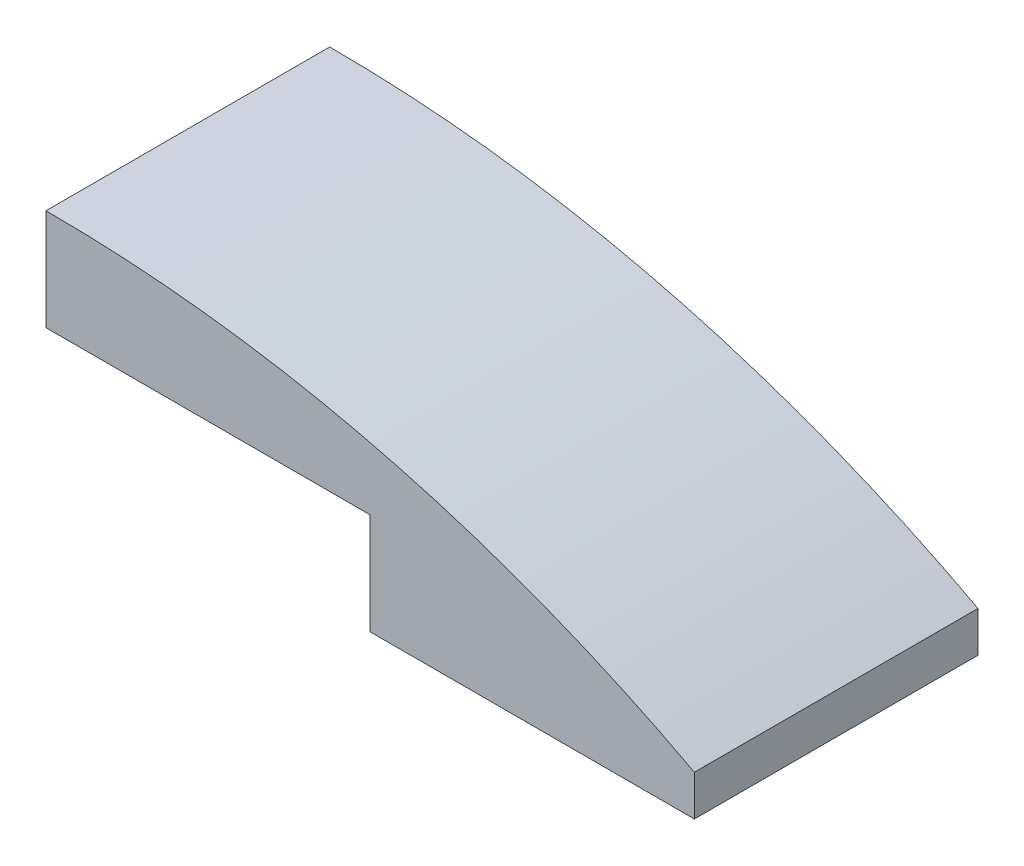
SolidWorks part; units mm, degrees
material "ABS"
ref_plane "Front Plane" through (0, 0, 0) normal (0, 0, 1) x (1, 0, 0)
ref_plane "Top Plane" through (0, 0, 0) normal (0, 1, 0) x (1, 0, 0)
ref_plane "Right Plane" through (0, 0, 0) normal (1, 0, 0) x (0, 0, -1)
sketch "Sketch1" plane through (0, 0, 0) normal (0, 0, 1) x (1, 0, 0)
  line L0 (-10.16, 0) -> (-10.16, 3.175)
  line L1 (-10.16, 0) -> (0, 0)
  line L2 (0, 0) -> (0, -3.175)
  line L3 (0, -3.175) -> (10.16, -3.175)
  line L4 (10.16, -3.175) -> (10.16, -1.905)
  arc A2 (-10.16, 3.175) -> (10.16, -1.905) centre (-10.16, -40.005) cw
  dimension "D1" = 3.175
  dimension "D2" = 20.32
  dimension "D3" = 10.16
  dimension "D4" = 1.27
extrude "Boss-Extrude1" add sketch "Sketch1" along normal mid plane 8.89
sketch "Sketch2" plane through (0, 0, 0) normal (0, -1, 0) x (1, 0, 0)
  line L0 (0, 4.1275) -> (-9.8425, 4.1275)
  line L1 (0, 4.445) -> (0, -4.445) construction
  line L2 (-9.8425, 4.1275) -> (-9.8425, -4.1275)
  line L3 (-9.8425, -4.1275) -> (0, -4.1275)
  line L4 (-10.16, 4.445) -> (0, 4.445) construction
  line L5 (-10.16, 4.445) -> (-10.16, -4.445) construction
  line L6 (-10.16, -4.445) -> (0, -4.445) construction
  line L7 (0, 4.1275) -> (0, -4.1275)
  dimension "D1" = 0.3175
  dimension "D2" = 0.3175
  dimension "D3" = 0.3175
extrude "Cut-Extrude1" cut sketch "Sketch2" against normal offset from surface (0.6548 mm away) 1.27
sketch "Sketch3" plane through (0, -3.175, 0) normal (0, -1, 0) x (1, 0, 0)
  line L8 (0.3175, -4.1275) -> (9.8425, -4.1275)
  line L9 (9.8425, 4.1275) -> (9.8425, -4.1275)
  line L10 (0.3175, 4.1275) -> (9.8425, 4.1275)
  line L11 (0.3175, 4.1275) -> (0.3175, -4.1275)
extrude "Cut-Extrude3" cut sketch "Sketch3" against normal offset from surface (0.1676 mm away) 1.27
ref_plane "Plane1" through (0, -5.08, 0) normal (0, 1, 0) x (1, 0, 0)
sketch "Sketch4" plane through (0, -5.08, 0) normal (0, 1, 0) x (1, 0, 0)
  line L0 (-10.16, -4.445) -> (0, 4.445) construction
  line L1 (0, -4.445) -> (10.16, 4.445) construction
  circle A0 centre (-5.08, 0) radius 2.54
  circle A1 centre (5.08, 0) radius 2.54
  circle A2 centre (5.08, 0) radius 1.905
  circle A3 centre (-5.08, 0) radius 1.905
  dimension "D1" = 5.08
  dimension "D2" = 3.81
extrude "Boss-Extrude2" add sketch "Sketch4" along normal up to next
sketch "Sketch5" plane through (0, 0, 0) normal (0, 0, 1) x (1, 0, 0)
  line L0 (4.8895, -5.08) -> (-4.8895, -5.08) construction
  line L1 (-1.7412, -1.905) -> (-7.9443, -1.905)
  line L2 (-1.7412, -1.905) -> (-1.7412, -5.08)
  line L3 (-1.7412, -5.08) -> (-7.9443, -5.08)
  line L4 (-7.9443, -1.905) -> (-7.9443, -5.08)
  line L5 (-10.16, 0) -> (0, 0) construction
  dimension "D1" = 1.905
extrude "Cut-Extrude4" cut sketch "Sketch5" against normal through all both and the other way through all
